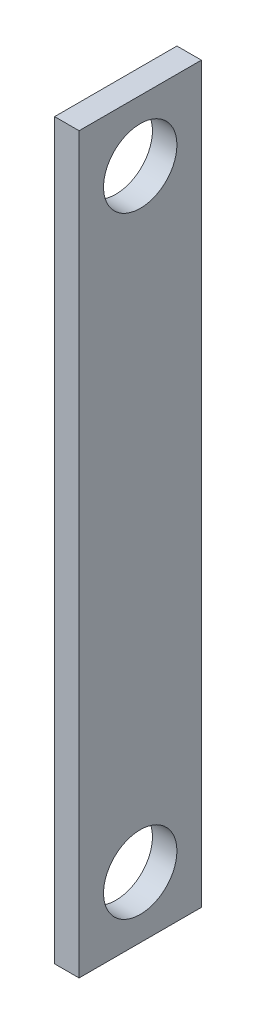
SolidWorks part; units mm, degrees
ref_plane "Front Plane" through (0, 0, 0) normal (0, 0, 1) x (1, 0, 0)
ref_plane "Top Plane" through (0, 0, 0) normal (0, 1, 0) x (1, 0, 0)
ref_plane "Right Plane" through (0, 0, 0) normal (1, 0, 0) x (0, 0, -1)
sketch "Sketch1" plane through (0, 0, 0) normal (1, 0, 0) x (0, 0, -1)
  line L1 (-5, -30) -> (5, -30)
  line L2 (-5, -30) -> (-5, 30)
  line L3 (-5, 30) -> (5, 30)
  line L4 (5, -30) -> (5, 30)
  line L5 (-5, -30) -> (5, 30) construction
  line L6 (-5, 30) -> (5, -30) construction
  point P0 (0, 0)
  dimension "D1" = 60
  dimension "D2" = 10
extrude "Boss-Extrude1" add sketch "Sketch1" along normal blind 2
sketch "Sketch2" plane through (2, 0, 0) normal (1, 0, 0) x (0, 0, -1)
  circle A0 centre (0, -25) radius 3
  circle A1 centre (0, 25) radius 3
  dimension "D3" = 6
  dimension "D4" = 6
  dimension "D1" = 25
  dimension "D2" = 25
extrude "Cut-Extrude1" cut sketch "Sketch2" against normal up to surface (2 mm away) up to face at (0, 0, 0)
